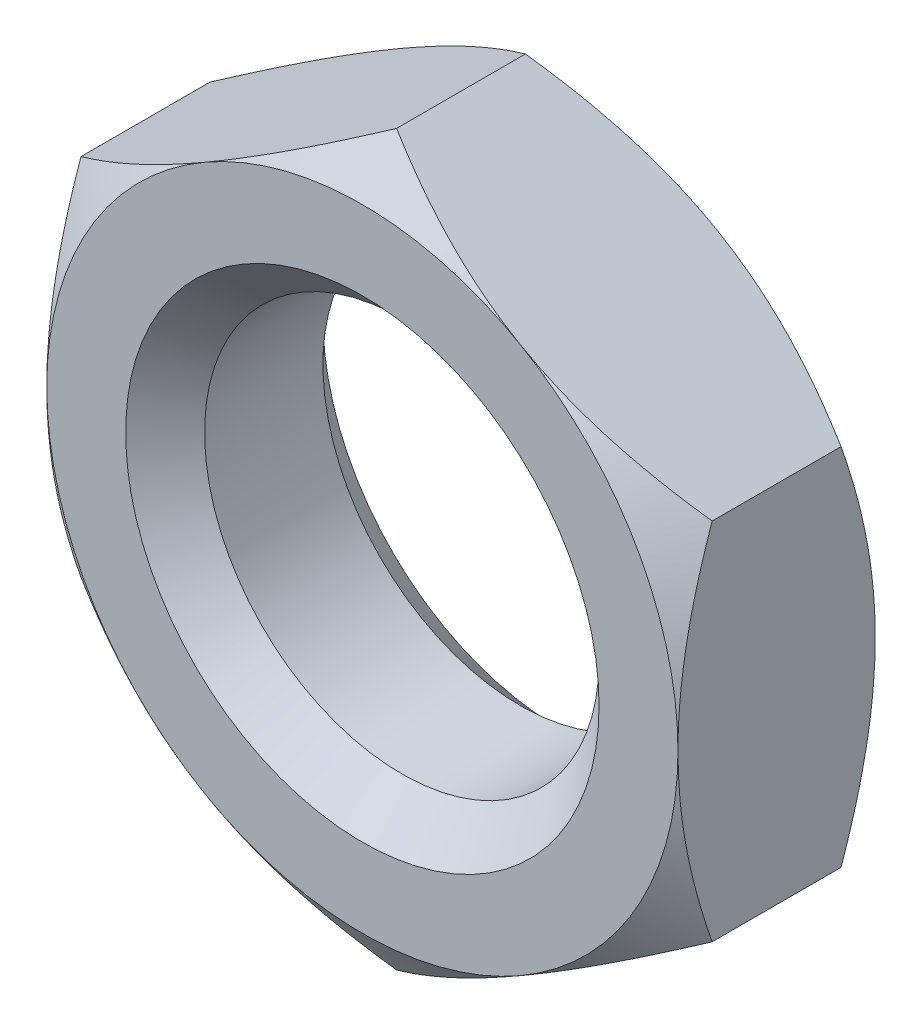
SolidWorks part; units mm, degrees
ref_plane "Front Plane" through (0, 0, 0) normal (0, 0, 1) x (1, 0, 0)
ref_plane "Top Plane" through (0, 0, 0) normal (0, 1, 0) x (1, 0, 0)
ref_plane "Right Plane" through (0, 0, 0) normal (1, 0, 0) x (0, 0, -1)
sketch "Sketch1" plane through (0, 0, 0) normal (0, 0, 1) x (1, 0, 0)
  line L1 (-8, 4.6188) -> (-8, -4.6188)
  line L2 (-8, -4.6188) -> (0, -9.2376)
  line L3 (0, -9.2376) -> (8, -4.6188)
  line L4 (8, -4.6188) -> (8, 4.6188)
  line L5 (8, 4.6188) -> (0, 9.2376)
  line L6 (0, 9.2376) -> (-8, 4.6188)
  circle A0 centre (0, 0) radius 8 construction
  circle A1 centre (0, 0) radius 5
  dimension "D2" = 10
  dimension "D1" = 16
extrude "Boss-Extrude1" add sketch "Sketch1" along normal mid plane 5
sketch "Sketch2" plane through (0, 0, 2.5) normal (0, 0, 1) x (1, 0, 0)
  line L0 (0, 9.2376) -> (-8, 4.6188) construction
  circle A0 centre (0, 0) radius 8
extrude "Cut-Extrude1" cut sketch "Sketch2" against normal through all draft 55 flip side to cut
mirror "Mirror1" about plane through (0, 0, 0) normal (0, 0, 1) of "Cut-Extrude1"
chamfer "Chamfer1" distance 1 angle 45 2 edges at (5, 0, -2.5) (5, 0, 2.5)
